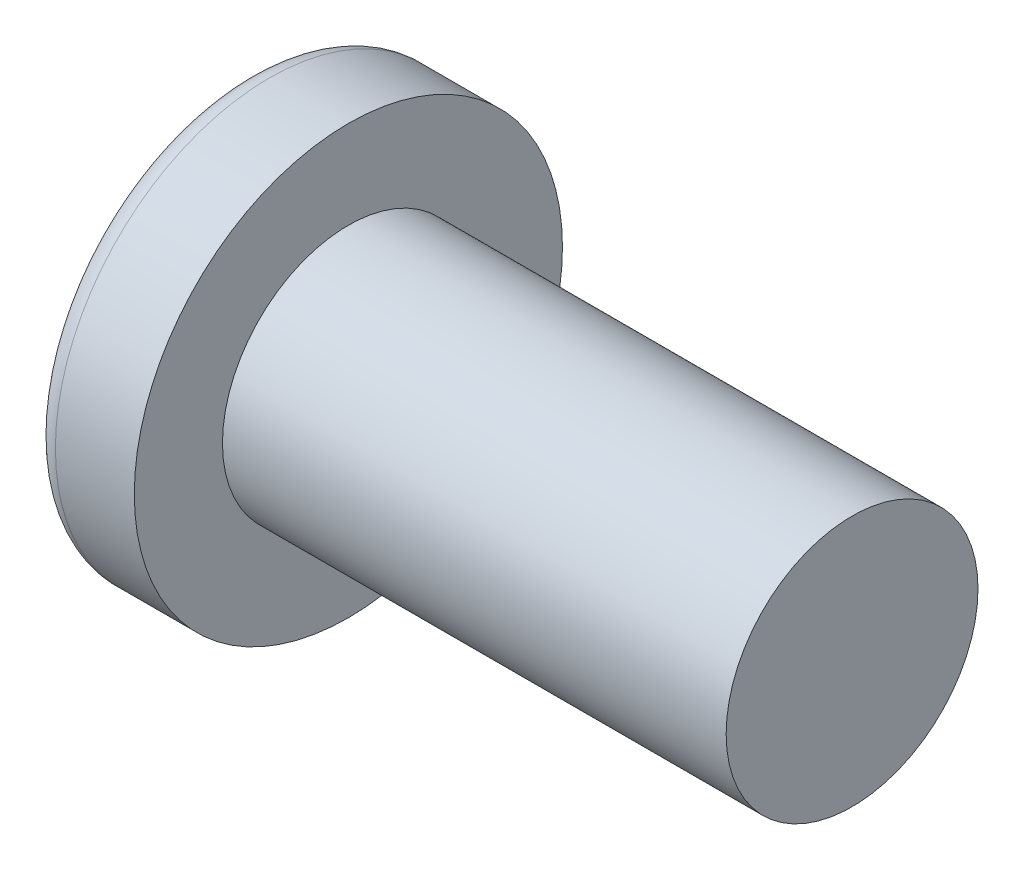
SolidWorks part; units mm, degrees
ref_plane "Ön Düzlem" through (0, 0, 0) normal (0, 0, 1) x (1, 0, 0)
ref_plane "Üst Düzlem" through (0, 0, 0) normal (0, 1, 0) x (1, 0, 0)
ref_plane "Sağ Düzlem" through (0, 0, 0) normal (1, 0, 0) x (0, 0, -1)
sketch "Çizim1" plane through (0, 0, 0) normal (0, 1, 0) x (1, 0, 0)
  line L0 (-7.8, 0) -> (0, 0)
  line L1 (0, 0) -> (0, 1.5)
  line L2 (0, 1.5) -> (-6, 1.5)
  line L3 (-6, 1.5) -> (-6, 2.55)
  line L4 (-6, 2.55) -> (-6.94, 2.55)
  arc A0 (-6.94, 2.55) -> (-7.2008, 2.3499) centre (-6.94, 2.28) ccw
  arc A1 (-7.2008, 2.3499) -> (-7.8, 0) centre (-3.2875, 0.1007) ccw
revolve "Döndür1" add sketch "Çizim1" angle 360 about L0
ref_plane "Düzlem1" through (-8, 0, 0) normal (1, 0, 0) x (0, 0, -1)
